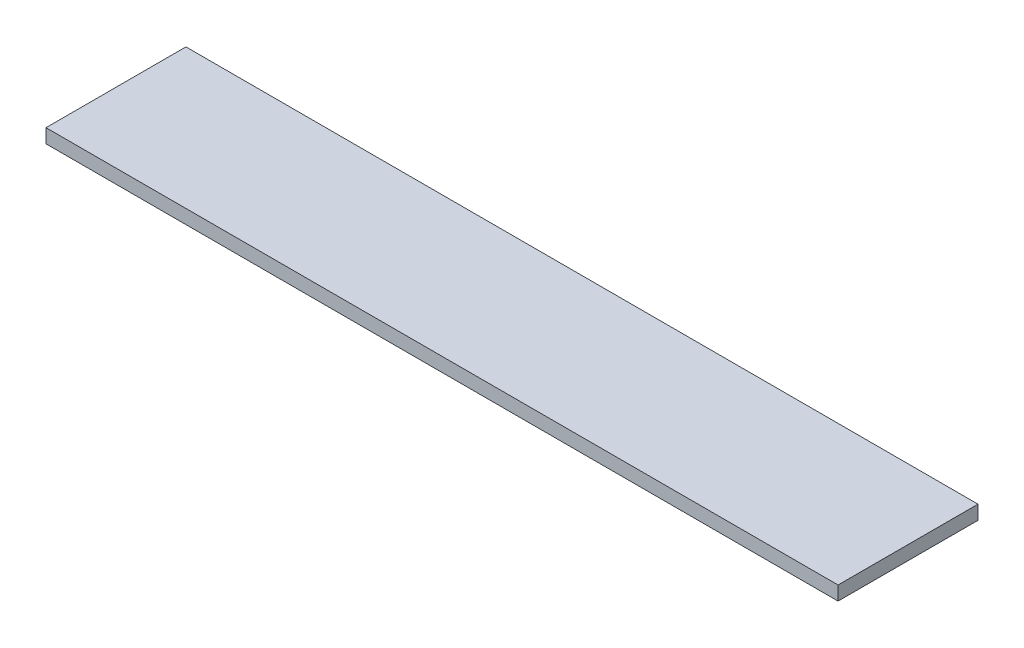
SolidWorks part; units mm, degrees
ref_plane "Face" through (0, 0, 0) normal (0, 0, 1) x (1, 0, 0)
ref_plane "Dessus" through (0, 0, 0) normal (0, 1, 0) x (1, 0, 0)
ref_plane "Droite" through (0, 0, 0) normal (1, 0, 0) x (0, 0, -1)
sketch "Esquisse1" plane through (0, 0, 0) normal (0, 1, 0) x (1, 0, 0)
  line L1 (0, 0) -> (566, 0)
  line L2 (0, 0) -> (0, 100)
  line L3 (0, 100) -> (566, 100)
  line L4 (566, 0) -> (566, 100)
  dimension "D1" = 566
  dimension "D2" = 100
extrude "Extrusion1" add sketch "Esquisse1" along normal blind 10
